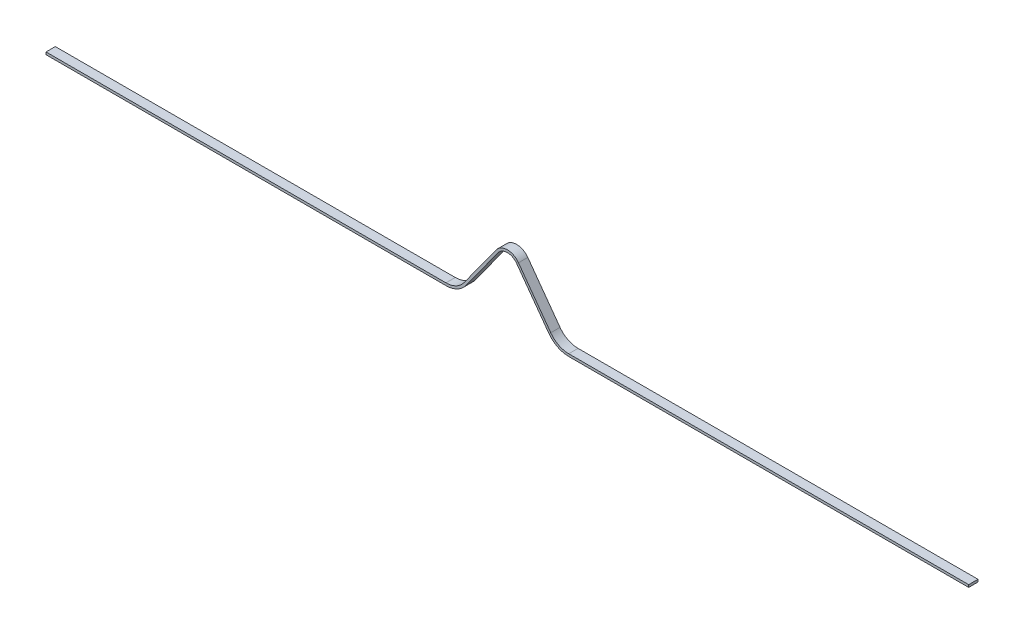
SolidWorks part; units mm, degrees
material "Rubber"
ref_plane "Front Plane" through (0, 0, 0) normal (0, 0, 1) x (1, 0, 0)
ref_plane "Top Plane" through (0, 0, 0) normal (0, 1, 0) x (1, 0, 0)
ref_plane "Right Plane" through (0, 0, 0) normal (1, 0, 0) x (0, 0, -1)
sketch "Sketch1" plane through (0, 0, 0) normal (0, 0, 1) x (1, 0, 0)
  line L0 (0, 0) -> (0, -12.55) construction
  line L1 (0, -12.55) -> (-33, -12.55) construction
  line L2 (-248, -24.5) -> (-33, -24.5)
  line L3 (-23.3253, -19.5645) -> (-5.991, 4.3437)
  line L4 (248, -24.5) -> (33, -24.5)
  line L5 (23.3253, -19.5645) -> (5.991, 4.3437)
  arc A0 (5.991, 4.3437) -> (-5.991, 4.3437) centre (0, 0) ccw
  arc A1 (-33, -24.5) -> (-23.3253, -19.5645) centre (-33, -12.55) ccw
  arc A2 (33, -24.5) -> (23.3253, -19.5645) centre (33, -12.55) cw
  dimension "D3" = 23.9
  dimension "D4" = 14.8
  dimension "D1" = 12.55
  dimension "D2" = 33
  dimension "D5" = 248
  dimension "D6" = 248
extrude "Extrude-Thin1" add sketch "Sketch1" along normal mid plane 5 thin
